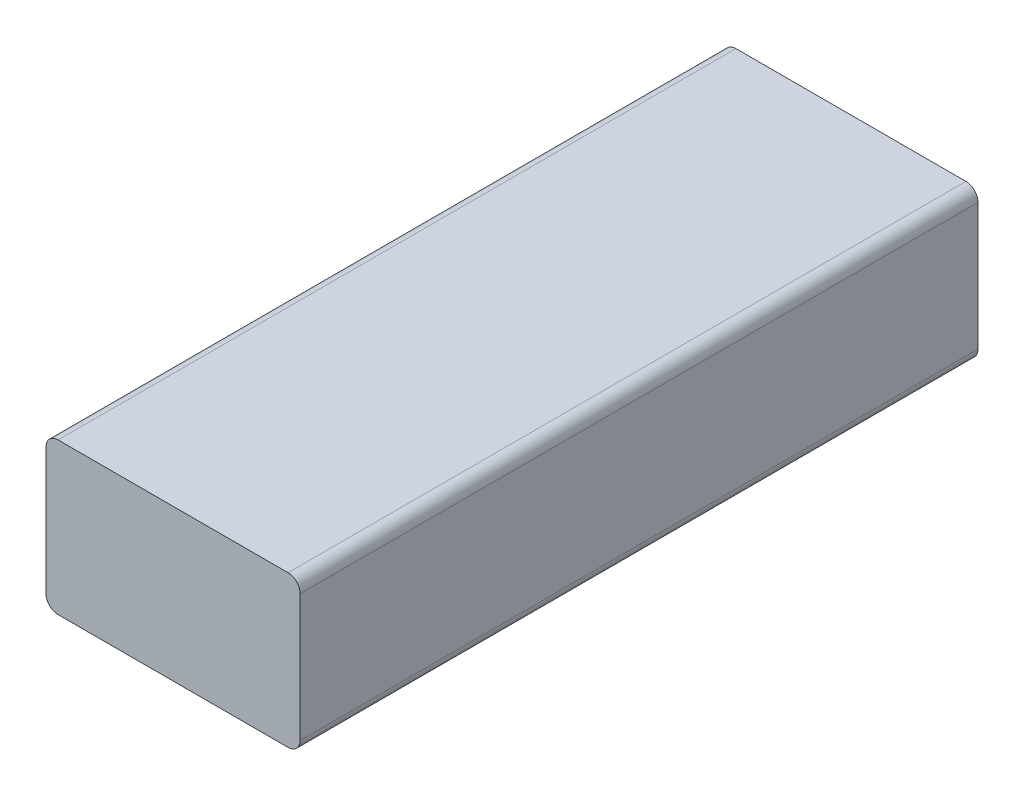
SolidWorks part; units mm, degrees
material "Polyurethane Foam Rigid"
ref_plane "Front Plane" through (0, 0, 0) normal (0, 0, 1) x (1, 0, 0)
ref_plane "Top Plane" through (0, 0, 0) normal (0, 1, 0) x (1, 0, 0)
ref_plane "Right Plane" through (0, 0, 0) normal (1, 0, 0) x (0, 0, -1)
sketch "Sketch1" plane through (0, 0, 0) normal (0, 0, 1) x (1, 0, 0)
  line L1 (-29.3403, 15.8854) -> (12.6597, 15.8854)
  line L2 (-29.3403, 15.8854) -> (-29.3403, -9.1146)
  line L3 (-29.3403, -9.1146) -> (12.6597, -9.1146)
  line L4 (12.6597, 15.8854) -> (12.6597, -9.1146)
  dimension "D1" = 25
  dimension "D2" = 42
extrude "Boss-Extrude1" add sketch "Sketch1" against normal blind 112
fillet "Fillet1" radius 2 4 edges at (12.6597, -9.1146, -56) (12.6597, 15.8854, -56) (-29.3403, -9.1146, -56) (-29.3403, 15.8854, -56)
